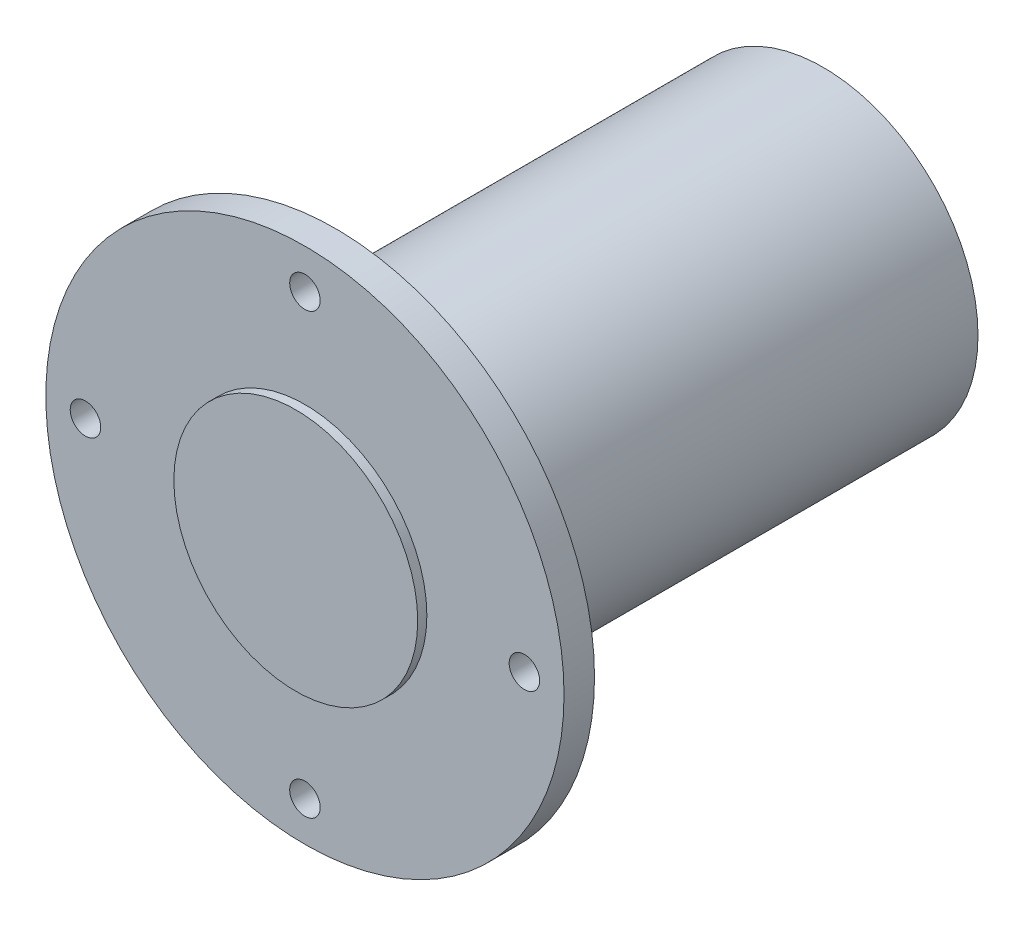
SolidWorks part; units mm, degrees
material "6061 Alloy"
ref_plane "Front Plane" through (0, 0, 0) normal (0, 0, 1) x (1, 0, 0)
ref_plane "Top Plane" through (0, 0, 0) normal (0, 1, 0) x (1, 0, 0)
ref_plane "Right Plane" through (0, 0, 0) normal (1, 0, 0) x (0, 0, -1)
sketch "Sketch1" plane through (0, 0, 0) normal (0, 0, 1) x (1, 0, 0)
  circle A0 centre (0, 0) radius 42.5
  dimension "D1" = 85
extrude "Boss-Extrude1" add sketch "Sketch1" along normal blind 5
sketch "Sketch4" plane through (0, 0, 0) normal (0, 0, -1) x (-1, 0, 0)
  circle A0 centre (0, 0) radius 25.4
  dimension "D1" = 50.8
extrude "Boss-Extrude2" add sketch "Sketch4" along normal blind 80
sketch "Sketch5" plane through (0, 0, -80) normal (0, 0, -1) x (-1, 0, 0)
  circle A0 centre (0, 0) radius 20.4
  circle A1 centre (0, 0) radius 25.4 construction
  dimension "D1" = 5
extrude "Cut-Extrude1" cut sketch "Sketch5" against normal blind 70
fillet "Fillet1" radius 5 1 edges at (-25.4, 0, 0)
hole_wizard "M6x1.0 Tapped Hole1" positions "Sketch6" profile "Sketch7" tap size "M6x1.0" standard "ANSI Metric" end condition up to next
sketch "Sketch6" plane through (0, 0, 0) normal (0, 0, -1) x (-1, 0, 0)
  line L0 (0, 46.75) -> (0, -46.75) construction
  line L1 (46.75, 0) -> (-46.75, 0) construction
  circle A0 centre (0, 0) radius 36
  point P0 (0, 36)
  point P4 (36, 0)
  point P8 (0, -36)
  point P10 (-36, 0)
  point P17 (0, 0)
  point P18 (0, 0)
  point P19 (0, 0)
  point P20 (0, 0)
  point P21 (0, 0)
  point P22 (0, 0)
  dimension "D1" = 72
sketch "Sketch7" plane through (0, 36, 0) normal (1, 0, 0) x (0, 1, 0)
  line L0 (0, 0) -> (0, 5)
  line L1 (0, 5) -> (2.5, 5)
  line L2 (2.5, 5) -> (2.5, 0)
  line L5 (2.5, 0) -> (0, 0)
  line L11 (0, -6.35) -> (0, 107.95) construction
  dimension "Thru Tap Drill Dia." = 5
  dimension "Thru Tap Drill Depth" = 5
cosmetic thread "Hole Thread1" parameters "D2"=6
cosmetic thread "Hole Thread2" parameters "D2"=6
cosmetic thread "Hole Thread3" parameters "D2"=6
cosmetic thread "Hole Thread4" parameters "D2"=6
sketch "Sketch8" plane through (0, 0, 5) normal (0, 0, 1) x (1, 0, 0)
  circle A0 centre (0, 0) radius 20
  dimension "D1" = 40
extrude "Boss-Extrude3" add sketch "Sketch8" along normal blind 1.5
